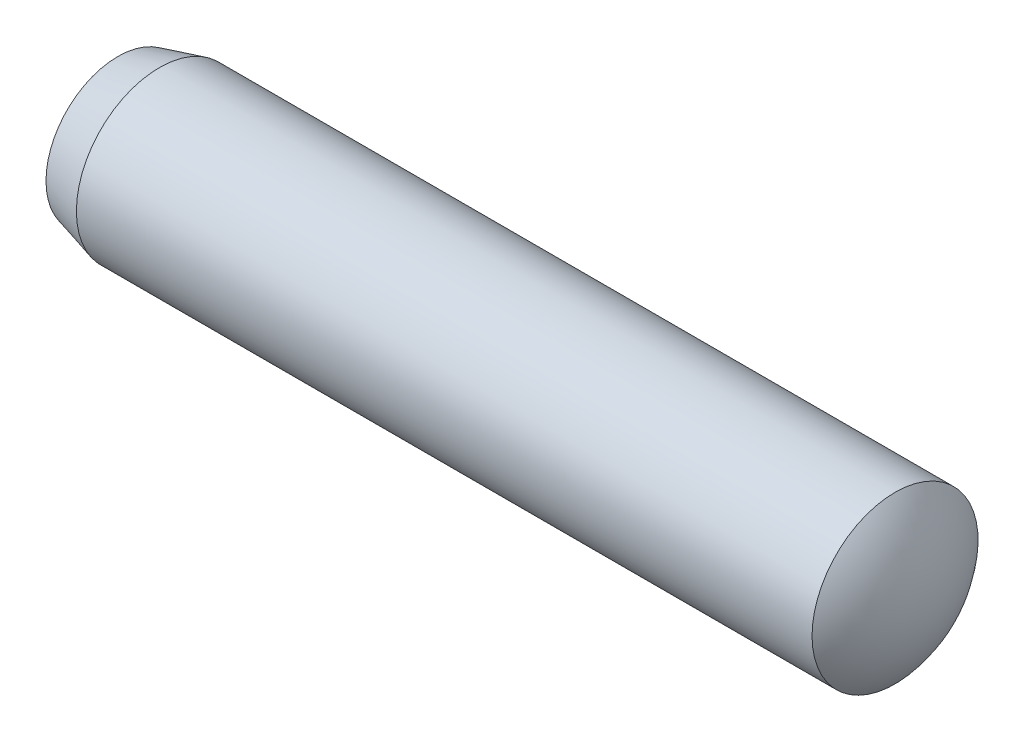
SolidWorks part; units mm, degrees
ref_plane "Front" through (0, 0, 0) normal (0, 0, 1) x (1, 0, 0)
ref_plane "Top" through (0, 0, 0) normal (0, 1, 0) x (1, 0, 0)
ref_plane "Right" through (0, 0, 0) normal (1, 0, 0) x (0, 0, -1)
sketch "Support-Front" plane through (0, 0, 0) normal (0, 0, 1) x (1, 0, 0)
  line L0 (1.5352, 0) -> (10, 0) construction
  line L1 (0.2676, 0.866) -> (0.7676, 1)
  line L2 (0.2676, -0.866) -> (0.7676, -1)
  line L3 (0.7676, 1) -> (9.6296, 1)
  line L4 (0.7676, -1) -> (9.6296, -1)
  line L5 (0.7676, 1) -> (0.7676, -1) construction
  line L6 (10, -1) -> (10, 1) construction
  line L7 (10, 1) -> (9.6296, 1) construction
  line L8 (10, -1) -> (9.6296, -1) construction
  line L9 (10, 0) -> (9.6296, 1) construction
  line L10 (1.5352, 0) -> (0.7676, 0) construction
  line L11 (0.7676, 0) -> (0, 0) construction
  line L12 (0.7676, 0) -> (0.2676, 0.866) construction
  arc A0 (0.2676, 0.866) -> (0.2676, -0.866) centre (1.5352, 0) ccw
  arc A1 (9.6296, -1) -> (9.6296, 1) centre (8.4648, 0) ccw
  dimension "D1" = 15
  dimension "D2" = 30
  dimension "Diam" = 2
  dimension "Length" = 10
sketch "Sketch2" plane through (0, 0, 0) normal (0, 0, 1) x (1, 0, 0)
  line L3 (1.5352, 0) -> (10, 0) construction
  line L4 (0.7676, 1) -> (9.6296, 1) construction
  line L5 (0.2676, 0.866) -> (0.7676, 1) construction
  line L6 (1.5352, 0) -> (10, 0) construction
  line L7 (0.7676, 1) -> (9.6296, 1)
  line L8 (0.2676, 0.866) -> (0.7676, 1)
  line L9 (1.5352, 0) -> (10, 0)
  line L10 (0.7676, 0) -> (0, 0) construction
  line L11 (1.5352, 0) -> (0.7676, 0) construction
  line L12 (0.7676, 0) -> (0, 0) construction
  line L13 (1.5352, 0) -> (0.7676, 0) construction
  line L14 (1.5352, 0) -> (0, 0)
  arc A2 (9.6296, -1) -> (9.6296, 1) centre (8.4648, 0) ccw construction
  arc A4 (10, 0) -> (9.6296, 1) centre (8.4648, 0) ccw
  circle A5 centre (1.5352, 0) radius 1.5352 construction
  arc A6 (0.2676, 0.866) -> (0, 0) centre (1.5352, 0) ccw
revolve "Body" add sketch "Sketch2" angle 360 about L6
